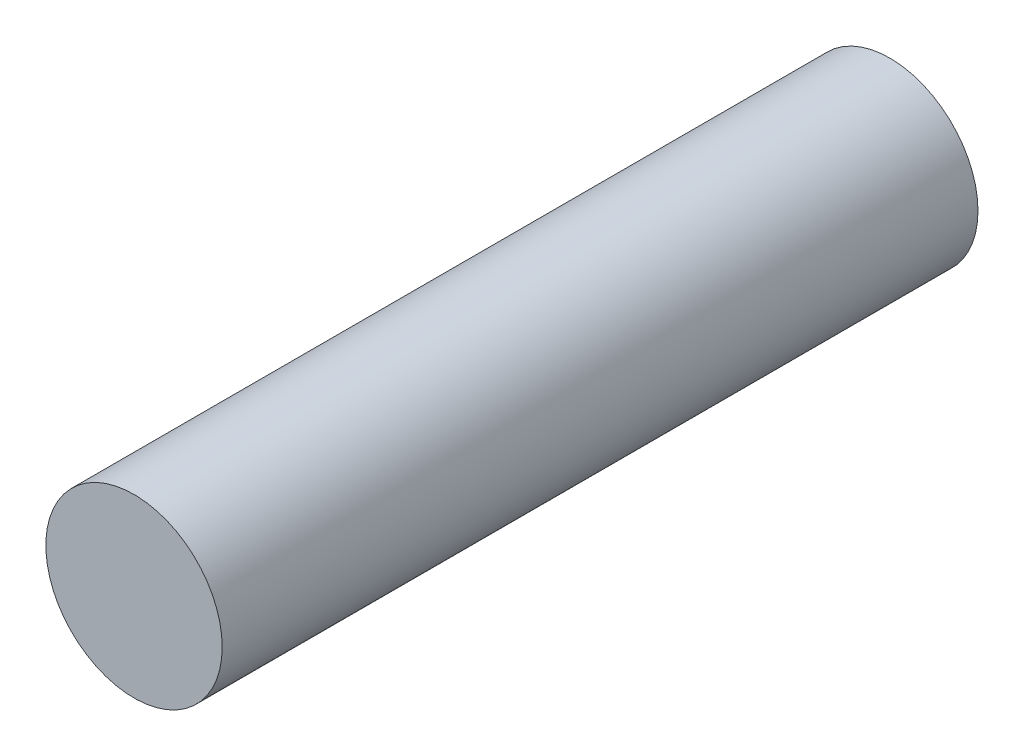
SolidWorks part; units mm, degrees
ref_plane "Front Plane" through (0, 0, 0) normal (0, 0, 1) x (1, 0, 0)
ref_plane "Top Plane" through (0, 0, 0) normal (0, 1, 0) x (1, 0, 0)
ref_plane "Right Plane" through (0, 0, 0) normal (1, 0, 0) x (0, 0, -1)
sketch "Sketch1" plane through (0, 0, 0) normal (0, 0, 1) x (1, 0, 0)
  circle A0 centre (0, 0) radius 0.35
  dimension "D1" = 0.7
extrude "Boss-Extrude1" add sketch "Sketch1" along normal blind 3
